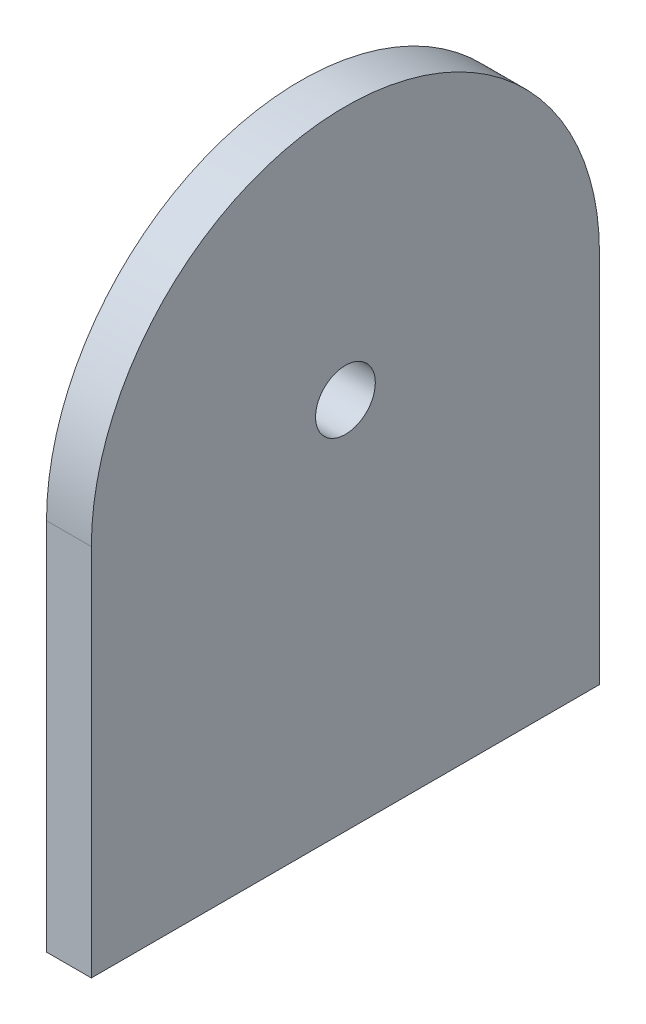
SolidWorks part; units mm, degrees
ref_plane "Alzado" through (0, 0, 0) normal (0, 0, 1) x (1, 0, 0)
ref_plane "Planta" through (0, 0, 0) normal (0, 1, 0) x (1, 0, 0)
ref_plane "Vista lateral" through (0, 0, 0) normal (1, 0, 0) x (0, 0, -1)
sketch "Croquis1" plane through (0, 0, 0) normal (1, 0, 0) x (0, 0, -1)
  line L0 (0, 0) -> (34, 0)
  line L1 (34, 25) -> (34, 0)
  line L2 (0, 0) -> (0, 25)
  arc A0 (34, 25) -> (0, 25) centre (17, 25) ccw
  circle A1 centre (17, 25) radius 2
  dimension "D1" = 4
  dimension "D3" = 25
  dimension "D4" = 34
extrude "Saliente-Extruir1" add sketch "Croquis1" along normal blind 3
